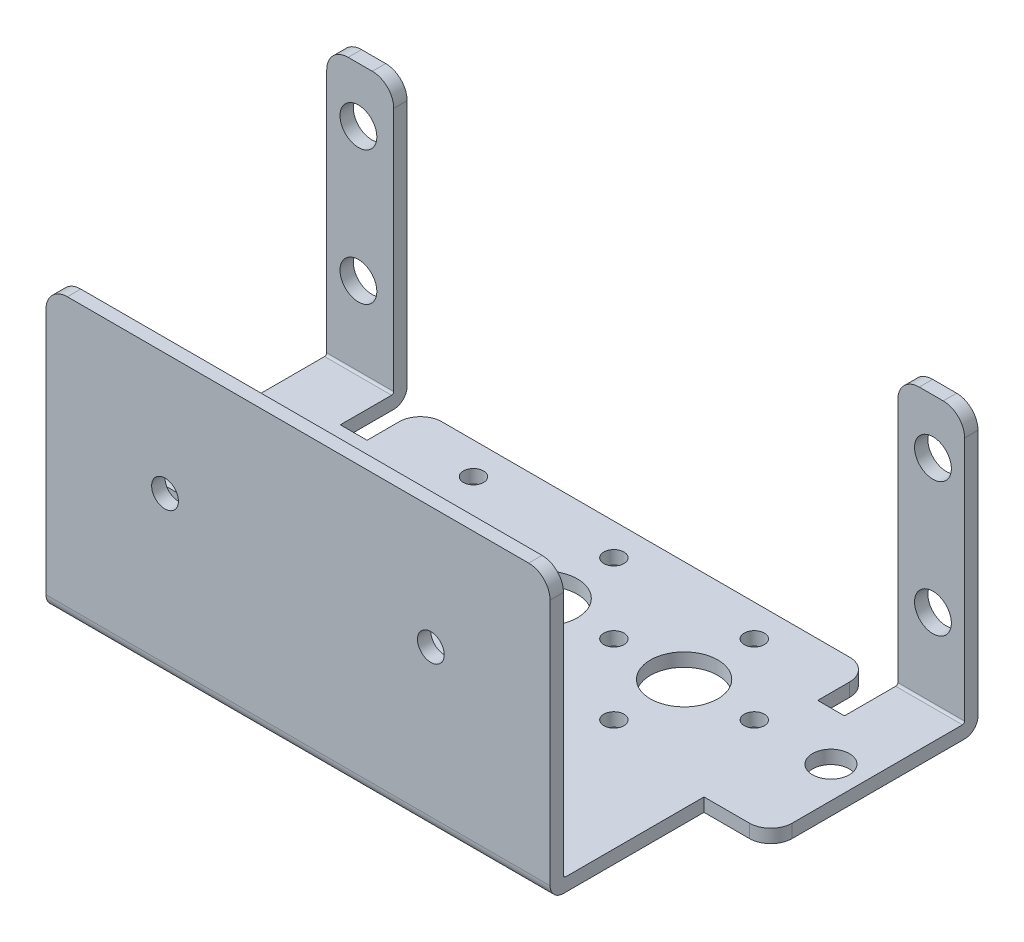
SolidWorks part; units mm, degrees
ref_plane "Front Plane" through (0, 0, 0) normal (0, 0, 1) x (1, 0, 0)
ref_plane "Top Plane" through (0, 0, 0) normal (0, 1, 0) x (1, 0, 0)
ref_plane "Right Plane" through (0, 0, 0) normal (1, 0, 0) x (0, 0, -1)
sketch "Sketch1" plane through (0, 0, 0) normal (1, 0, 0) x (0, 0, -1)
  line L0 (1.5875, 33.4772) -> (1.5875, 1.5875)
  line L1 (1.5875, 0) -> (41.2623, 0)
  line L2 (0, 1.5875) -> (0, 33.4772)
  line L3 (0, 33.4772) -> (1.5875, 33.4772)
  line L4 (42.8498, 1.5875) -> (42.8498, 33.4772)
  line L5 (1.5875, 1.5875) -> (41.2623, 1.5875)
  line L6 (41.2623, 1.5875) -> (41.2623, 33.4772)
  line L7 (41.2623, 33.4772) -> (42.8498, 33.4772)
  arc A0 (1.5875, 0) -> (0, 1.5875) centre (1.5875, 1.5875) cw
  arc A1 (41.2623, 0) -> (42.8498, 1.5875) centre (41.2623, 1.5875) ccw
  point P11 (0, 0)
  point P14 (42.8498, 0)
  dimension "D6" = 1.5875
  dimension "D1" = 33.4772
  dimension "D2" = 42.8498
  dimension "D3" = 1.5875
  dimension "D4" = 1.5875
  dimension "D5" = 1.5875
extrude "Extrude1" add sketch "Sketch1" along normal blind 75.692
sketch "Sketch2" plane through (0, 33.4772, 0) normal (0, 1, 0) x (1, 0, 0)
  line L0 (75.692, 0) -> (0, 0) construction
  line L1 (0, 0) -> (7.9502, 0)
  line L2 (0, 0) -> (0, 18.2626)
  line L3 (0, 18.2626) -> (7.9502, 18.2626)
  line L4 (7.9502, 0) -> (7.9502, 18.2626)
  line L5 (67.7672, 0) -> (75.692, 0)
  line L6 (67.7672, 0) -> (67.7672, 18.2626)
  line L7 (67.7672, 18.2626) -> (75.692, 18.2626)
  line L8 (75.692, 0) -> (75.692, 18.2626)
  line L9 (75.692, 41.2623) -> (75.692, 1.5875) construction
  line L10 (0, 41.2623) -> (0, 1.5875) construction
  dimension "D1" = 7.9502
  dimension "D2" = 18.2626
  dimension "D3" = 67.7672
  dimension "D4" = 18.2626
extrude "Extrude2" cut sketch "Sketch2" against normal up to surface (33.4772 mm away) up to face at (37.846, 0, -21.4249)
sketch "Sketch3" plane through (0, 1.5875, 0) normal (0, 1, 0) x (1, 0, 0)
  line L0 (75.692, 42.8498) -> (0, 42.8498) construction
  line L1 (7.9502, 42.8498) -> (67.7672, 42.8498)
  line L2 (7.9502, 42.8498) -> (7.9502, 41.2623)
  line L3 (7.9502, 41.2623) -> (67.7672, 41.2623)
  line L4 (67.7672, 42.8498) -> (67.7672, 41.2623)
  line L5 (75.692, 41.2623) -> (0, 41.2623) construction
  line L6 (0, 41.2623) -> (0, 18.2626) construction
  dimension "D1" = 7.9502
  dimension "D2" = 67.7672
extrude "Extrude3" cut sketch "Sketch3" along normal up to surface and the other way up to surface up to face at (37.846, 33.4772, -42.056) other way up to face at (37.8524, 0, -19.8438)
sketch "Sketch4" plane through (0, 1.5875, 0) normal (0, 1, 0) x (1, 0, 0)
  line L0 (67.7672, 0) -> (7.9502, 0) construction
  line L1 (7.9502, 41.2623) -> (11.1252, 41.2623)
  line L2 (7.9502, 41.2623) -> (7.9502, 34.925)
  line L3 (7.9502, 34.925) -> (11.1252, 34.925)
  line L4 (11.1252, 41.2623) -> (11.1252, 34.925)
  line L5 (0, 41.2623) -> (0, 18.2626) construction
  line L7 (67.7672, 41.2623) -> (64.5922, 41.2623)
  line L8 (67.7672, 41.2623) -> (67.7672, 34.925)
  line L9 (67.7672, 34.925) -> (64.5922, 34.925)
  line L10 (64.5922, 41.2623) -> (64.5922, 34.925)
  dimension "D1" = 34.925
  dimension "D2" = 11.1252
  dimension "D3" = 34.925
  dimension "D4" = 64.5922
extrude "Extrude4" cut sketch "Sketch4" against normal up to surface (1.5875 mm away) up to face at (37.8536, 0, -24.1275)
sketch "Sketch5" plane through (0, 1.5875, 0) normal (0, 1, 0) x (1, 0, 0)
  line L0 (67.7672, 0) -> (7.9502, 0) construction
  line L1 (0, 41.2623) -> (0, 18.2626) construction
  circle A0 centre (21.1836, 29.1592) radius 4.0005
  circle A1 centre (21.1836, 29.1592) radius 8.3312 construction
  circle A2 centre (21.1836, 37.4904) radius 1.1938
  circle A3 centre (12.8524, 29.1592) radius 1.1938
  circle A4 centre (21.1836, 20.828) radius 1.1938
  circle A5 centre (37.846, 37.4904) radius 1.1938
  circle A6 centre (37.846, 29.1592) radius 8.3312 construction
  circle A7 centre (29.5148, 29.1592) radius 1.1938
  circle A8 centre (37.846, 20.828) radius 1.1938
  circle A9 centre (37.846, 29.1592) radius 4.0005
  circle A10 centre (54.5084, 20.828) radius 1.1938
  circle A11 centre (54.5084, 29.1592) radius 8.3312 construction
  circle A12 centre (54.5084, 29.1592) radius 4.0005
  circle A13 centre (46.1772, 29.1592) radius 1.1938
  circle A14 centre (54.5084, 37.4904) radius 1.1938
  circle A15 centre (62.8396, 29.1592) radius 1.1938
  circle A16 centre (3.7592, 29.1592) radius 2.1844
  circle A17 centre (71.9328, 29.1592) radius 2.1844
  dimension "D1" = 29.1592
  dimension "D3" = 16.6624
  dimension "D4" = 2.3876
  dimension "D5" = 8.001
  dimension "D6" = 3.7592
  dimension "D7" = 4.3688
  dimension "D2" = 21.1836
  dimension "D8" = 71.9328
extrude "Extrude5" cut sketch "Sketch5" against normal up to surface (1.5875 mm away) up to face at (37.8555, 0, -28.9687)
sketch "Sketch6" plane through (0, 0, 0) normal (0, 0, 1) x (1, 0, 0)
  line L0 (67.7672, 0) -> (7.9502, 0) construction
  line L1 (0, 33.4772) -> (0, 1.5875) construction
  circle A0 centre (3.7592, 27.0002) radius 2.1844
  circle A1 centre (3.7592, 11.1252) radius 2.1844
  circle A2 centre (71.9328, 27.0002) radius 2.1844
  circle A3 centre (71.9328, 11.1252) radius 2.1844
  circle A4 centre (22.0726, 19.05) radius 1.5875
  circle A5 centre (53.6194, 19.05) radius 1.5875
  point P16 (0, 17.5323)
  dimension "D1" = 11.1252
  dimension "D5" = 3.175
  dimension "D6" = 3.175
  dimension "D2" = 27.0002
  dimension "D3" = 3.7592
  dimension "D4" = 71.9328
  dimension "D7" = 19.05
  dimension "D8" = 22.0726
  dimension "D9" = 53.6194
extrude "Extrude6" cut sketch "Sketch6" against normal through all
fillet "Fillet1" radius 2.54 7 edges at (11.1252, 0.7937, -41.2623) (75.692, 0.7937, -18.2626) (7.9502, 33.4772, -0.7937) (67.7672, 33.4772, -0.7937) (0, 33.4772, -42.056) (75.692, 33.4772, -42.056) (64.5922, 0.7937, -41.2623)
fillet "Fillet2" radius 0.254 3 edges at (3.9751, 1.5875, -41.2623) (71.7296, 1.5875, -41.2623) (37.8587, 1.5875, -1.5875)
fillet "Fillet3" radius 2.54 1 edges at (0, 0.7937, -18.2626)
fillet "Fillet4" radius 2.54 2 edges at (7.9502, 33.4772, -42.056) (67.7672, 33.4772, -42.056)
